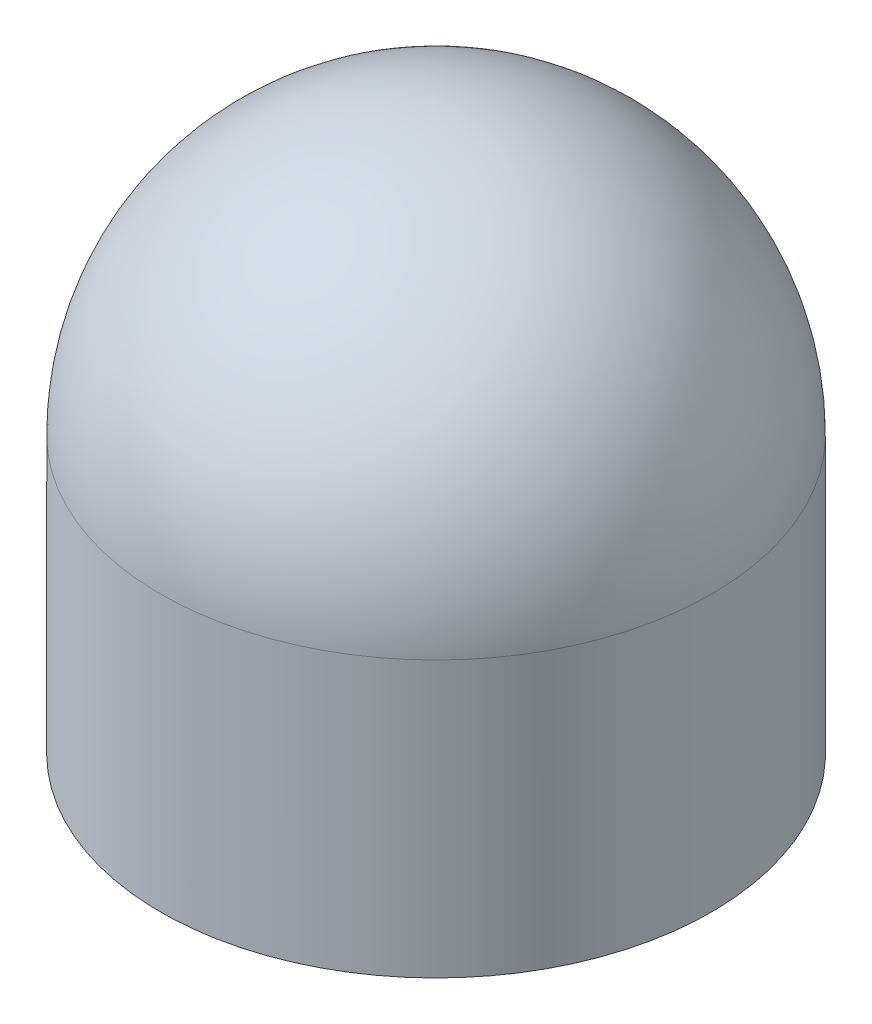
SolidWorks part; units mm, degrees
ref_plane "Front Plane" through (0, 0, 0) normal (0, 0, 1) x (1, 0, 0)
ref_plane "Top Plane" through (0, 0, 0) normal (0, 1, 0) x (1, 0, 0)
ref_plane "Right Plane" through (0, 0, 0) normal (1, 0, 0) x (0, 0, -1)
sketch "Sketch1" plane through (0, 0, 0) normal (0, 0, 1) x (1, 0, 0)
  line L0 (0, 0) -> (0, 12.7)
  line L1 (0, 0) -> (-6.35, 0)
  line L2 (-6.35, 0) -> (-6.35, 6.35)
  line L3 (0, 12.7) -> (11.8417, 12.7) construction
  arc A0 (-6.35, 6.35) -> (0, 12.7) centre (0, 6.35) cw
  dimension "D1" = 6.35
  dimension "D2" = 12.7
revolve "Revolve1" add sketch "Sketch1" angle 360 about L0
